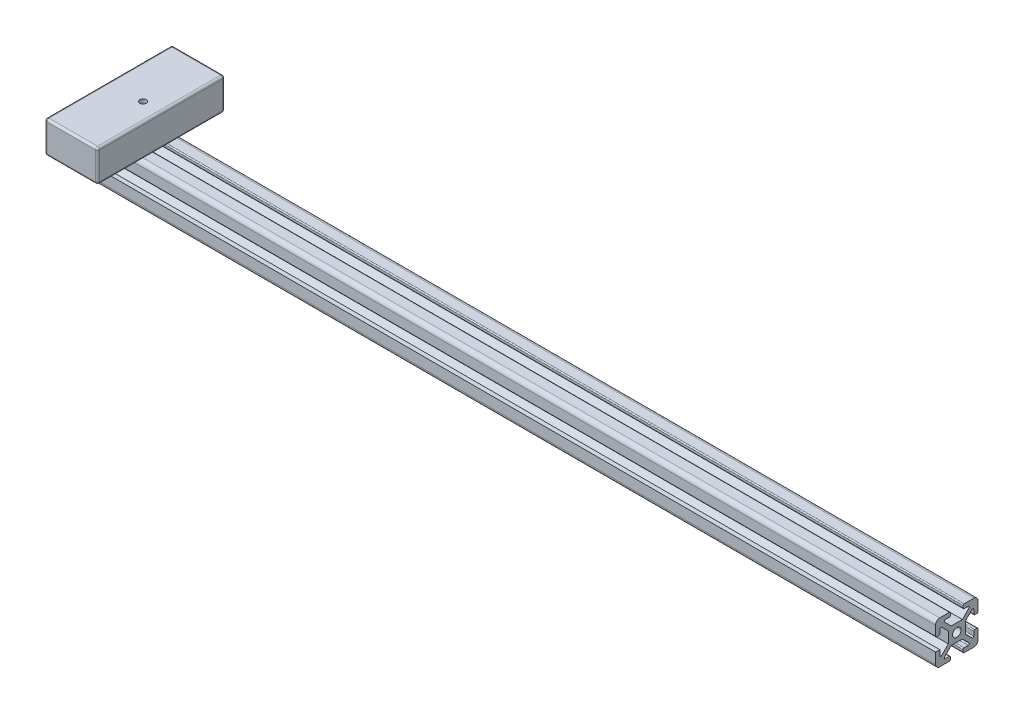
SolidWorks part; units mm, degrees
ref_plane "Front Plane" through (0, 0, 0) normal (0, 0, 1) x (1, 0, 0)
ref_plane "Top Plane" through (0, 0, 0) normal (0, 1, 0) x (1, 0, 0)
ref_plane "Right Plane" through (0, 0, 0) normal (1, 0, 0) x (0, 0, -1)
sketch "Sketch1" plane through (0, 0, 0) normal (0, 0, 1) x (1, 0, 0)
  line L0 (0, 0) -> (400, 0)
  dimension "D1" = 400
other "Aluminium profile 20×20(1)"
ref_plane "Plane1" through (0, 0, 0) normal (1, 0, 0) x (0, 1, 0)
sketch "Sketch2" plane through (0, 0, 0) normal (1, 0, 0) x (0, 1, 0)
  line L1 (-2.6666, -4) -> (2.6666, -4)
  line L2 (-4, -2.6502) -> (-4, 2.6502)
  line L3 (-2.6666, 4) -> (2.6666, 4)
  line L4 (4, -2.6502) -> (4, 2.6502)
  line L9 (3.4986, 10) -> (7.9986, 10) construction
  line L10 (9.9986, 3.5) -> (9.9986, 8) construction
  line L11 (4, 2.6502) -> (7.1467, 5.7673)
  line L12 (2.6666, 4) -> (5.7766, 7.1486)
  line L13 (9.9986, 8) -> (9.9986, 3.5)
  line L14 (9.4986, 3) -> (8.4986, 3)
  line L15 (7.9986, 3.5) -> (7.9986, 5.4121)
  line L16 (7.9986, 10) -> (3.4986, 10)
  line L17 (2.9986, 9.5) -> (2.9986, 8.5)
  line L18 (3.4986, 8) -> (5.4209, 8)
  line L20 (-9.9986, 3.5) -> (-9.9986, 8) construction
  line L21 (-2.9986, 10) -> (-7.9986, 10) construction
  line L23 (-2.9986, 8) -> (-5.4209, 8)
  line L24 (-2.9986, 10) -> (-2.9986, 8)
  line L25 (-7.9986, 10) -> (-2.9986, 10)
  line L26 (-7.9986, 3.5) -> (-7.9986, 5.4121)
  line L27 (-9.4986, 3) -> (-8.4986, 3)
  line L28 (-9.9986, 8) -> (-9.9986, 3.5)
  line L29 (-2.6666, 4) -> (-5.7766, 7.1486)
  line L30 (-4, 2.6502) -> (-7.1467, 5.7673)
  line L32 (-3.4986, -10) -> (-7.9986, -10) construction
  line L33 (-9.9986, -3.5) -> (-9.9986, -8) construction
  line L34 (9.9986, -3.5) -> (9.9986, -8) construction
  line L35 (3.4986, -10) -> (7.9986, -10) construction
  line L37 (-4, -2.6502) -> (-7.1467, -5.7673)
  line L38 (-2.6666, -4) -> (-5.7766, -7.1486)
  line L39 (-9.9986, -8) -> (-9.9986, -3.5)
  line L40 (-9.4986, -3) -> (-8.4986, -3)
  line L41 (-7.9986, -3.5) -> (-7.9986, -5.4121)
  line L42 (-7.9986, -10) -> (-3.4986, -10)
  line L43 (-2.9986, -9.5) -> (-2.9986, -8.5)
  line L44 (-3.4986, -8) -> (-5.4209, -8)
  line L45 (3.4986, -8) -> (5.4209, -8)
  line L46 (2.9986, -9.5) -> (2.9986, -8.5)
  line L47 (7.9986, -10) -> (3.4986, -10)
  line L48 (7.9986, -3.5) -> (7.9986, -5.4121)
  line L49 (9.4986, -3) -> (8.4986, -3)
  line L50 (9.9986, -8) -> (9.9986, -3.5)
  line L51 (2.6666, -4) -> (5.7766, -7.1486)
  line L52 (4, -2.6502) -> (7.1467, -5.7673)
  circle A0 centre (0, 0) radius 2
  arc A1 (7.9986, -10) -> (9.9986, -8) centre (7.9986, -8) ccw
  arc A2 (-9.9986, -8) -> (-7.9986, -10) centre (-7.9986, -8) ccw
  arc A3 (-7.9986, 10) -> (-9.9986, 8) centre (-7.9986, 8) ccw
  arc A4 (7.9986, 10) -> (9.9986, 8) centre (7.9986, 8) cw
  arc A5 (-9.4986, -3) -> (-9.9986, -3.5) centre (-9.4986, -3.5) ccw
  arc A6 (-8.4986, -3) -> (-7.9986, -3.5) centre (-8.4986, -3.5) cw
  arc A7 (-7.1467, -5.7673) -> (-7.9986, -5.4121) centre (-7.4986, -5.4121) cw
  arc A8 (-5.7766, -7.1486) -> (-5.4209, -8) centre (-5.4209, -7.5) ccw
  arc A9 (-2.9986, -9.5) -> (-3.4986, -10) centre (-3.4986, -9.5) cw
  arc A10 (-2.9986, -8.5) -> (-3.4986, -8) centre (-3.4986, -8.5) ccw
  arc A11 (7.9986, -5.4121) -> (7.1467, -5.7673) centre (7.4986, -5.4121) cw
  arc A12 (5.4209, -8) -> (5.7766, -7.1486) centre (5.4209, -7.5) ccw
  arc A13 (3.4986, -8) -> (2.9986, -8.5) centre (3.4986, -8.5) ccw
  arc A14 (3.4986, -10) -> (2.9986, -9.5) centre (3.4986, -9.5) cw
  arc A15 (9.9986, -3.5) -> (9.4986, -3) centre (9.4986, -3.5) ccw
  arc A16 (7.9986, -3.5) -> (8.4986, -3) centre (8.4986, -3.5) cw
  arc A17 (9.9986, 3.5) -> (9.4986, 3) centre (9.4986, 3.5) cw
  arc A18 (8.4986, 3) -> (7.9986, 3.5) centre (8.4986, 3.5) cw
  arc A19 (7.9986, 5.4121) -> (7.1467, 5.7673) centre (7.4986, 5.4121) ccw
  arc A20 (3.4986, 10) -> (2.9986, 9.5) centre (3.4986, 9.5) ccw
  arc A21 (2.9986, 8.5) -> (3.4986, 8) centre (3.4986, 8.5) ccw
  arc A22 (5.4209, 8) -> (5.7766, 7.1486) centre (5.4209, 7.5) cw
  arc A23 (-5.4209, 8) -> (-5.7766, 7.1486) centre (-5.4209, 7.5) ccw
  arc A24 (-7.9986, 5.4121) -> (-7.1467, 5.7673) centre (-7.4986, 5.4121) cw
  arc A25 (-7.9986, 3.5) -> (-8.4986, 3) centre (-8.4986, 3.5) cw
  arc A26 (-9.9986, 3.5) -> (-9.4986, 3) centre (-9.4986, 3.5) ccw
  point P7 (0, 0)
  point P84 (7.9986, 3)
  point P92 (2.9986, 8)
  dimension "D1" = 4
  dimension "D2" = 2
  dimension "D3" = 0.5
sketch "Sketch3" plane through (0, 0, 10) normal (0, 0, 1) x (1, 0, 0)
  line L2 (0, 0) -> (400, 0) construction
  circle A1 centre (364, 0) radius 2
  circle A2 centre (336, 0) radius 2
  point P0 (350, 0)
  dimension "D4" = 4
  dimension "D5" = 4
  dimension "D1" = 350
  dimension "D2" = 14
  dimension "D3" = 14
extrude "Cut-Extrude1" cut sketch "Sketch3" against normal blind 40
sketch "Sketch4" plane through (0, 9.9986, 0) normal (0, 1, 0) x (1, 0, 0)
  line L1 (24.879, 30) -> (0, 30)
  line L2 (24.879, 30) -> (24.879, -30)
  line L3 (24.879, -30) -> (0, -30)
  line L4 (0, 30) -> (0, -30)
  line L5 (24.879, 30) -> (0, -30) construction
  line L6 (24.879, -30) -> (0, 30) construction
  point P0 (12.4395, 0)
  dimension "D1" = 60
extrude "Boss-Extrude1" add sketch "Sketch4" along normal blind 15 separate body
fillet "Fillet1" radius 1 12 edges at (0, 17.4986, -30) (0, 17.4986, 30) (12.4395, 9.9986, 30) (12.4395, 9.9986, -30) (0, 9.9986, 0) (12.4395, 24.9986, -30) (12.4395, 24.9986, 30) (0, 24.9986, 0) (24.879, 17.4986, 30) (24.879, 24.9986, 0) (24.879, 17.4986, -30) (24.879, 9.9986, 0)
sketch "Sketch6" plane through (0, 24.9986, 0) normal (0, 1, 0) x (1, 0, 0)
  line L0 (0, 0) -> (16.3424, 0) construction
  circle A0 centre (16.3424, 0) radius 1.5
  dimension "D1" = 3
extrude "Cut-Extrude2" cut sketch "Sketch6" against normal blind 40
